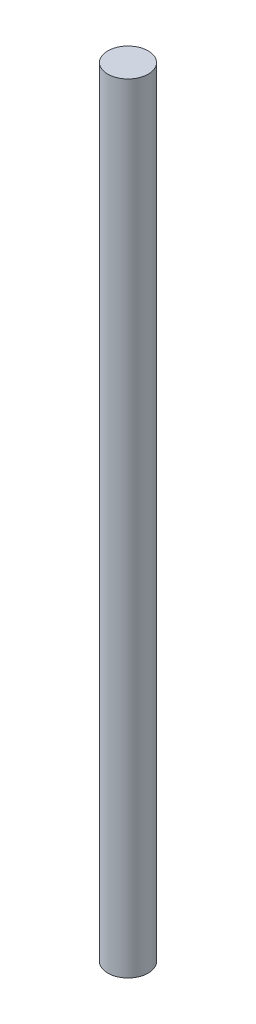
SolidWorks part; units mm, degrees
ref_plane "Front Plane" through (0, 0, 0) normal (0, 0, 1) x (1, 0, 0)
ref_plane "Top Plane" through (0, 0, 0) normal (0, 1, 0) x (1, 0, 0)
ref_plane "Right Plane" through (0, 0, 0) normal (1, 0, 0) x (0, 0, -1)
sketch "Sketch1" plane through (0, 0, 0) normal (0, 1, 0) x (1, 0, 0)
  circle A0 centre (0, 0) radius 1
  dimension "D1" = 2
extrude "Boss-Extrude1" add sketch "Sketch1" along normal blind 38.55 contours A0
